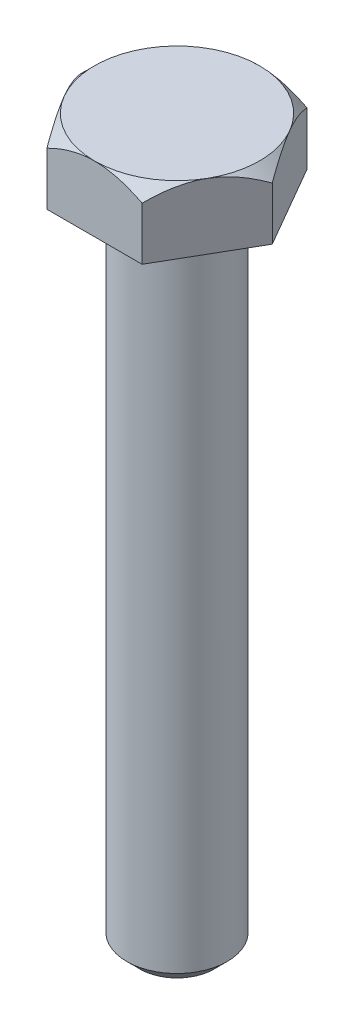
SolidWorks part; units mm, degrees
ref_plane "Спереди" through (0, 0, 0) normal (0, 0, 1) x (1, 0, 0)
ref_plane "Сверху" through (0, 0, 0) normal (0, 1, 0) x (1, 0, 0)
ref_plane "Справа" through (0, 0, 0) normal (1, 0, 0) x (0, 0, -1)
sketch "Эскиз6" plane through (0, 0, 0) normal (0, 1, 0) x (1, 0, 0)
  line L1 (7.25, 0) -> (3.625, 6.2787)
  line L2 (3.625, 6.2787) -> (-3.625, 6.2787)
  line L3 (-3.625, 6.2787) -> (-7.25, 0)
  line L4 (-7.25, 0) -> (-3.625, -6.2787)
  line L5 (-3.625, -6.2787) -> (3.625, -6.2787)
  line L6 (3.625, -6.2787) -> (7.25, 0)
  circle A0 centre (0, 0) radius 6.2787 construction
  dimension "D1" = 14.5
extrude "Бобышка-Вытянуть1" add sketch "Эскиз6" along normal blind 5
sketch "Эскиз8" plane through (0, 5, 0) normal (0, 1, 0) x (1, 0, 0)
  circle A0 centre (0, 0) radius 6.2787
extrude "Вырез-Вытянуть1" cut sketch "Эскиз8" against normal blind 1 draft 45 flip side to cut
sketch "Эскиз9" plane through (0, 0, 0) normal (0, -1, 0) x (1, 0, 0)
  circle A0 centre (0, 0) radius 3.825
  dimension "D1" = 7.65
extrude "bolt length" add sketch "Эскиз9" along normal blind 50
fillet "Скругление1" radius 1 1 edges at (0, 0, 3.825)
chamfer "Фаска1" distance 1 angle 45 1 edges at (0, -50, -3.825)
